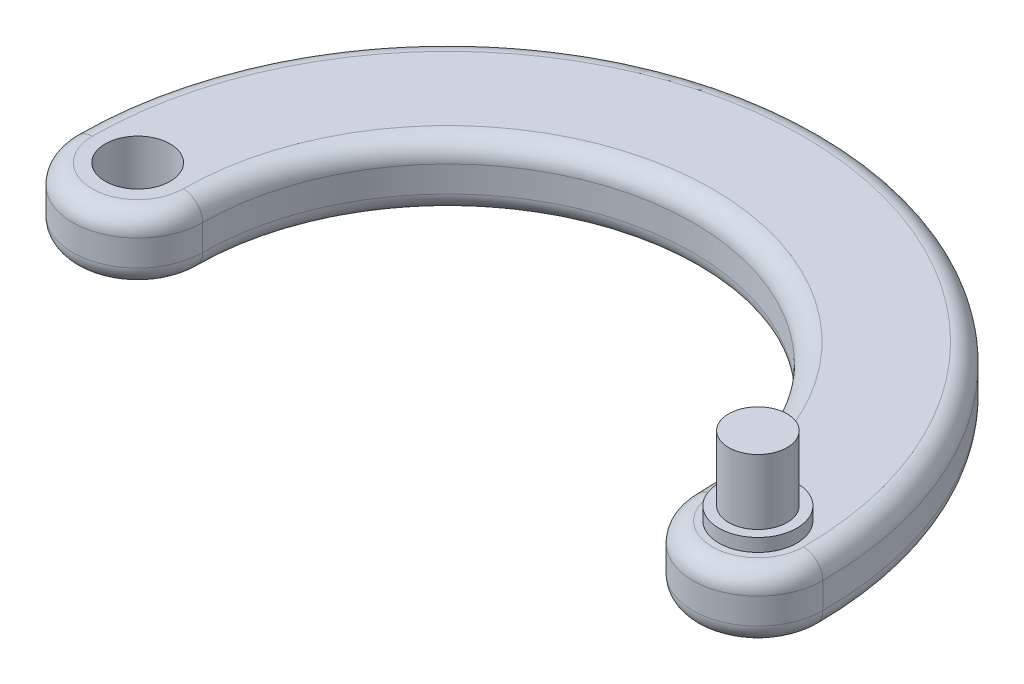
SolidWorks part; units mm, degrees
ref_plane "Front Plane" through (0, 0, 0) normal (0, 0, 1) x (1, 0, 0)
ref_plane "Top Plane" through (0, 0, 0) normal (0, 1, 0) x (1, 0, 0)
ref_plane "Right Plane" through (0, 0, 0) normal (1, 0, 0) x (0, 0, -1)
sketch "Sketch1" plane through (0, 0, 0) normal (0, 1, 0) x (1, 0, 0)
  circle A0 centre (-95.5, 0) radius 5
  circle A1 centre (0, 0) radius 5
  arc A2 (-10, 0) -> (10, 0) centre (0, 0) ccw
  arc A3 (-105.5, 0) -> (-85.5, 0) centre (-95.5, 0) ccw
  arc A4 (-10, 0) -> (-85.5, 0) centre (-47.75, 0) ccw
  arc A5 (10, 0) -> (-105.5, 0) centre (-47.75, 0) ccw
  circle A6 centre (-95.5, 0) radius 10 construction
  circle A7 centre (0, 0) radius 10 construction
  dimension "D1" = 5
extrude "Boss-Extrude1" add sketch "Sketch1" along normal blind 10
sketch "Sketch2" plane through (0, 10, 0) normal (0, 1, 0) x (1, 0, 0)
  circle A0 centre (0, 0) radius 4.5
extrude "Boss-Extrude2" add sketch "Sketch2" along normal blind 12 and the other way blind 10
sketch "Sketch3" plane through (0, 10, 0) normal (0, 1, 0) x (1, 0, 0)
  circle A0 centre (0, 0) radius 5
extrude "Boss-Extrude3" add sketch "Sketch3" against normal blind 10
sketch "Sketch4" plane through (0, 10, 0) normal (0, 1, 0) x (1, 0, 0)
  circle A0 centre (0, 0) radius 6
extrude "Boss-Extrude4" add sketch "Sketch4" along normal blind 2
fillet "Fillet1" radius 3 8 edges at (0, 0, 10) (-47.75, 0, -37.75) (-95.5, 0, 10) (0, 10, 10) (-47.75, 10, -37.75) (-95.5, 10, 10) (-47.75, 0, -57.75) (-47.75, 10, -57.75)
